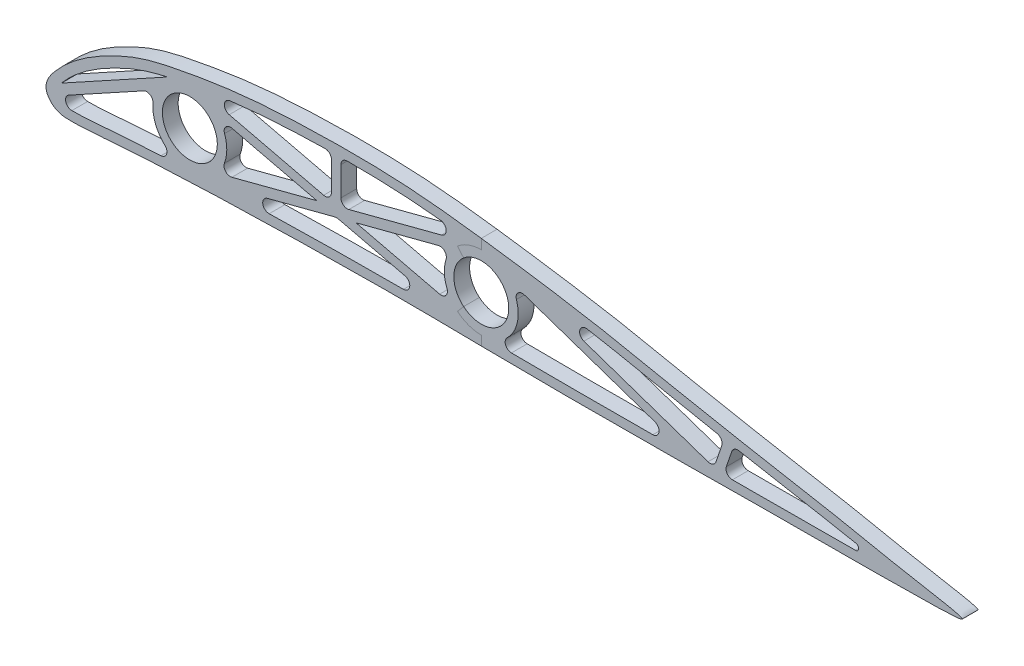
SolidWorks part; units mm, degrees
ref_plane "Front Plane" through (0, 0, 0) normal (0, 0, 1) x (1, 0, 0)
ref_plane "Top Plane" through (0, 0, 0) normal (0, 1, 0) x (1, 0, 0)
ref_plane "Right Plane" through (0, 0, 0) normal (1, 0, 0) x (0, 0, -1)
curve "Curve2"
  spline degree 3 poles (347.2078, -1.0359, 0) (378.9056, -0.7849, 0) (347.0347, 4.3271, 0) (326.8672, 8.8163, 0) (293.8899, 14.7227, 0) (257.5945, 21.3594, 0) (220.71, 29.3067, 0) (183.776, 34.7309, 0) (146.9268, 39.6342, 0) (109.9286, 39.8555, 0) (79.1221, 38.2217, 0) (54.6682, 34.1652, 0) (39.0987, 30.9157, 0) (27.0567, 25.6555, 0) (17.7869, 20.6913, 0) (10.0203, 15.09, 0) (3.6231, 8.8035, 0) (-2.539, 0.9573, 0) (3.8446, -5.5387, 0) (10.8213, -5.8955, 0) (18.4974, -5.5047, 0) (27.6862, -4.7118, 0) (39.9451, -3.8521, 0) (55.2855, -3.1527, 0) (79.8248, -2.2114, 0) (110.5105, -1.5148, 0) (147.3408, -1.1807, 0) (184.1821, -1.8502, 0) (220.968, -1.9589, 0) (257.9758, -1.783, 0) (294.1308, -1.2951, 0) (326.9075, -1.4474, 0) (347.2078, -1.0359, 0) (378.9056, -0.7849, 0) (347.0347, 4.3271, 0) knots -0.097522 -0.048769 -0.024396 0 0.025026 0.049952 0.099684 0.149416 0.199259 0.248703 0.297849 0.346623 0.395439 0.420071 0.445104 0.458263 0.47205 0.487006 0.495455 0.509299 0.518413 0.524589 0.536779 0.54899 0.561193 0.585585 0.609963 0.658715 0.707463 0.756228 0.804981 0.853734 0.902478 0.951231 0.975604 1 1.025026 1.049952 1.099684 periodic
sketch "Sketch2" plane through (0, 0, 0) normal (0, 0, 1) x (1, 0, 0)
  line L0 (336.0335, 6.748) -> (336.0335, 2.8594)
  line L2 (332.2235, 3.6512) -> (332.2235, 2.5181) construction
  line L3 (332.2235, 2.5181) -> (336.0335, 2.5612)
  line L4 (332.2235, 3.6512) -> (336.0335, 2.8594)
  line L5 (336.0335, 2.5612) -> (336.0335, -1.243)
  line L6 (336.0335, 6.748) -> (336.0335, -1.243) construction
  spline S0 degree 3 poles (347.2078, -1.0359) (378.9056, -0.7849) (347.0347, 4.3271) (326.8672, 8.8163) (293.8899, 14.7227) (257.5945, 21.3594) (220.71, 29.3067) (183.776, 34.7309) (146.9268, 39.6342) (109.9286, 39.8555) (79.1221, 38.2217) (54.6682, 34.1652) (39.0987, 30.9157) (27.0567, 25.6555) (17.7869, 20.6913) (10.0203, 15.09) (3.6231, 8.8035) (-2.539, 0.9573) (3.8446, -5.5387) (10.8213, -5.8955) (18.4974, -5.5047) (27.6862, -4.7118) (39.9451, -3.8521) (55.2855, -3.1527) (79.8248, -2.2114) (110.5105, -1.5148) (147.3408, -1.1807) (184.1821, -1.8502) (220.968, -1.9589) (257.9758, -1.783) (294.1308, -1.2951) (326.9075, -1.4474) (347.2078, -1.0359) (378.9056, -0.7849) (347.0347, 4.3271) knots -0.097522 -0.048769 -0.024396 0 0.025026 0.049952 0.099684 0.149416 0.199259 0.248703 0.297849 0.346623 0.395439 0.420071 0.445104 0.458263 0.47205 0.487006 0.495455 0.509299 0.518413 0.524589 0.536779 0.54899 0.561193 0.585585 0.609963 0.658715 0.707463 0.756228 0.804981 0.853734 0.902478 0.951231 0.975604 1 1.025026 1.049952 1.099684 only from (368.3, 0) to (368.3, 0) construction
  spline S1 degree 3 poles (336.0335, 6.748) (334.4682, 7.075) (322.1272, 9.6653) (293.8899, 14.7227) (257.5945, 21.3594) (220.71, 29.3067) (183.776, 34.7309) (146.9268, 39.6342) (109.9286, 39.8555) (79.1221, 38.2217) (54.6682, 34.1652) (39.0987, 30.9157) (27.0567, 25.6555) (17.7869, 20.6913) (10.0203, 15.09) (3.6231, 8.8035) (-2.539, 0.9573) (3.8446, -5.5387) (10.8213, -5.8955) (18.4974, -5.5047) (27.6862, -4.7118) (39.9451, -3.8521) (55.2855, -3.1527) (79.8248, -2.2114) (110.5105, -1.5148) (147.3408, -1.1807) (184.1821, -1.8502) (220.968, -1.9589) (257.9758, -1.783) (294.1308, -1.2951) (322.154, -1.4253) (334.5116, -1.2646) (336.0335, -1.243) knots 0.042905 0.042905 0.042905 0.042905 0.049952 0.099684 0.149416 0.199259 0.248703 0.297849 0.346623 0.395439 0.420071 0.445104 0.458263 0.47205 0.487006 0.495455 0.509299 0.518413 0.524589 0.536779 0.54899 0.561193 0.585585 0.609963 0.658715 0.707463 0.756228 0.804981 0.853734 0.902478 0.951231 0.95793 0.95793 0.95793 0.95793
  spline S2 degree 1 poles (332.2235, 3.6512) (332.2235, 2.5181) knots 0 0 1 1 construction
  spline S3 degree 3 poles (332.2235, 3.6512) (331.4422, 3.8136) (329.8922, 4.1334) (326.6834, 4.7813) (322.5372, 5.5957) (317.3751, 6.5801) (310.3118, 7.8973) (301.2497, 9.5464) (290.3993, 11.5032) (279.8146, 13.4324) (269.3583, 15.3818) (258.9524, 17.3888) (245.0217, 20.2063) (227.5735, 23.8306) (206.6663, 27.516) (185.5957, 30.5651) (164.4612, 33.491) (143.4609, 35.515) (125.8553, 35.9183) (111.6987, 35.7516) (97.5326, 35.338) (83.4604, 34.4409) (69.558, 32.7373) (59.1489, 31.0158) (48.6966, 29.0654) (40.4092, 26.9524) (34.112, 24.5762) (29.4067, 22.4489) (24.7943, 20.1232) (20.3602, 17.5841) (16.7827, 15.2133) (14.0746, 13.1936) (12.14, 11.6239) (10.3374, 10.022) (8.8926, 8.6048) (7.7177, 7.3643) (6.5041, 6.0281) (5.094, 4.3284) (4.135, 2.7508) (3.7669, 1.7737) (3.6718, 1.2421) (3.687, 0.9354) (3.7569, 0.6641) (4.0378, 0.131) (4.6772, -0.6496) (5.6338, -1.3432) (6.4413, -1.6604) (7.2188, -1.8332) (8.1959, -1.9275) (9.4011, -1.9594) (10.6859, -1.9678) (12.3801, -1.9489) (14.5213, -1.8763) (17.9805, -1.6803) (22.3734, -1.3453) (27.7107, -0.9045) (34.8675, -0.3821) (43.8089, 0.1382) (54.5116, 0.6135) (65.1973, 1.0423) (75.8958, 1.4157) (86.5937, 1.7244) (100.8575, 2.0599) (118.6805, 2.3593) (140.0876, 2.5332) (161.5153, 2.3652) (182.8671, 2.0367) (204.1695, 1.8943) (225.5342, 1.8895) (243.3798, 1.9622) (257.562, 2.0721) (268.1295, 2.1811) (278.734, 2.2927) (289.4592, 2.3847) (300.4526, 2.4262) (309.6907, 2.428) (316.9209, 2.4346) (322.2225, 2.4467) (326.4945, 2.4674) (329.8143, 2.493) (331.4156, 2.509) (332.2235, 2.5181) knots 0.047492 0.047492 0.047492 0.047492 0.051027 0.054562 0.061631 0.0687 0.07577 0.089908 0.104047 0.118186 0.132325 0.146463 0.160602 0.18888 0.217157 0.245434 0.273712 0.301989 0.330267 0.344405 0.358544 0.386822 0.40096 0.415099 0.429238 0.443376 0.450446 0.457515 0.464585 0.471654 0.478723 0.482258 0.485793 0.489327 0.492862 0.494629 0.496397 0.499931 0.503466 0.505233 0.507001 0.508768 0.510535 0.512303 0.51407 0.517605 0.519372 0.521139 0.522907 0.524674 0.526441 0.528209 0.531743 0.535278 0.542347 0.549417 0.556486 0.570625 0.584764 0.598902 0.613041 0.62718 0.641319 0.669596 0.697873 0.726151 0.754428 0.782706 0.810983 0.839261 0.853399 0.867538 0.881677 0.895815 0.909954 0.924093 0.931162 0.938232 0.945301 0.948836 0.95237 0.95237 0.95237 0.95237
  dimension "D2" = 3.81
extrude "MainRibEdge" add sketch "Sketch2" along normal blind 6.35
sketch "Sketch3" plane through (0, 0, 6.35) normal (0, 0, 1) x (1, 0, 0)
  line L0 (336.0335, 6.748) -> (336.0335, -1.243)
  spline S0 degree 3 poles (347.2078, -1.0359) (378.9056, -0.7849) (347.0347, 4.3271) (326.8672, 8.8163) (293.8899, 14.7227) (257.5945, 21.3594) (220.71, 29.3067) (183.776, 34.7309) (146.9268, 39.6342) (109.9286, 39.8555) (79.1221, 38.2217) (54.6682, 34.1652) (39.0987, 30.9157) (27.0567, 25.6555) (17.7869, 20.6913) (10.0203, 15.09) (3.6231, 8.8035) (-2.539, 0.9573) (3.8446, -5.5387) (10.8213, -5.8955) (18.4974, -5.5047) (27.6862, -4.7118) (39.9451, -3.8521) (55.2855, -3.1527) (79.8248, -2.2114) (110.5105, -1.5148) (147.3408, -1.1807) (184.1821, -1.8502) (220.968, -1.9589) (257.9758, -1.783) (294.1308, -1.2951) (326.9075, -1.4474) (347.2078, -1.0359) (378.9056, -0.7849) (347.0347, 4.3271) knots -0.097522 -0.048769 -0.024396 0 0.025026 0.049952 0.099684 0.149416 0.199259 0.248703 0.297849 0.346623 0.395439 0.420071 0.445104 0.458263 0.47205 0.487006 0.495455 0.509299 0.518413 0.524589 0.536779 0.54899 0.561193 0.585585 0.609963 0.658715 0.707463 0.756228 0.804981 0.853734 0.902478 0.951231 0.975604 1 1.025026 1.049952 1.099684 only from (368.3, 0) to (368.3, 0) construction
  spline S1 degree 3 poles (336.0335, -1.243) (340.0487, -1.1859) (350.0854, -1.0131) (378.9056, -0.7849) (350.0555, 3.8426) (340.005, 5.9184) (336.0335, 6.748) knots 0.95793 0.95793 0.95793 0.95793 0.975604 1 1.025026 1.042905 1.042905 1.042905 1.042905
extrude "TrailingEdge" add sketch "Sketch3" against normal blind 6.35
curve "Curve3"
  spline degree 3 poles (368.3, 0, 0) (362.1489, 1.3722, 0) (349.8713, 4.1111, 0) (325.2364, 8.9405, 0) (294.4435, 14.6806, 0) (257.4457, 21.3707, 0) (220.7495, 29.3036, 0) (183.7655, 34.7317, 0) (146.9295, 39.6339, 0) (109.9284, 39.8556, 0) (79.1207, 38.2216, 0) (54.6708, 34.1654, 0) (39.0905, 30.9151, 0) (27.0719, 25.6565, 0) (17.7236, 20.6872, 0) (10.231, 15.1036, 0) (3.1002, 8.7697, 0) (1.1877, 3.3596, 0) (0, 0, 0) knots 0 0 0 0 0.049139 0.09808 0.195728 0.293375 0.391241 0.488324 0.584822 0.680589 0.776437 0.824803 0.873954 0.899793 0.926862 0.956228 0.972818 1 1 1 1
curve "Curve4"
  spline degree 3 poles (0, 0, 0) (1.3411, -2.0747, 0) (3.5909, -5.5551, 0) (10.9428, -5.8876, 0) (18.4563, -5.5073, 0) (27.697, -4.7111, 0) (39.9389, -3.8525, 0) (55.2876, -3.1526, 0) (79.8237, -2.2115, 0) (110.5102, -1.5147, 0) (147.3434, -1.1809, 0) (184.1719, -1.8495, 0) (221.006, -1.9618, 0) (257.8337, -1.7722, 0) (294.6611, -1.3355, 0) (325.3463, -1.3285, 0) (349.9126, -1.2419, 0) (362.169, -0.4141, 0) (368.3, 0, 0) knots 0 0 0 0 0.018575 0.03116 0.056003 0.080886 0.105755 0.155463 0.205144 0.304495 0.40384 0.503218 0.602571 0.701924 0.80126 0.900613 0.950284 1 1 1 1
sketch "Sketch4" plane through (0, 0, 6.35) normal (0, 0, 1) x (1, 0, 0)
  circle A0 centre (57.717, 15.6105) radius 11.049
  circle A1 centre (57.717, 15.6105) radius 14.859
  circle A2 centre (174.9061, 17.0255) radius 11.049
  circle A4 centre (174.9061, 17.0255) radius 14.859
  spline S2 degree 3 poles (-1571.0958, -3668.5405) (-88.2173, 232.2354) (-14.5428, 28.2276) (4.264, 0.4587) (4.5107, 0.113) (4.9792, -0.4876) (5.2009, -0.742) (5.6043, -1.1472) (5.7849, -1.2973) (6.0163, -1.4571) (6.0869, -1.4998) (6.218, -1.5696) (6.2738, -1.5952) (6.5055, -1.6837) (6.7297, -1.7469) (7.3085, -1.8487) (7.6611, -1.8872) (8.4582, -1.9367) (8.9036, -1.948) (11.2732, -1.982) (13.1149, -1.9349) (15.8918, -1.8) (16.8198, -1.7443) (18.6946, -1.6194) (19.6412, -1.5506) (22.497, -1.3333) (24.4247, -1.1735) (27.3326, -0.9419) (28.3045, -0.8665) (30.2445, -0.7212) (31.2138, -0.651) (36.0591, -0.3127) (39.9362, -0.0847) (47.6854, 0.3119) (51.5566, 0.4823) (59.2863, 0.8059) (63.1514, 0.9589) (74.7494, 1.3838) (82.4858, 1.6176) (97.9554, 1.9959) (105.6888, 2.1426) (121.1575, 2.3706) (128.8957, 2.4488) (140.5079, 2.4812) (144.3799, 2.4777) (152.1235, 2.4375) (155.9925, 2.4015) (167.5916, 2.27) (175.3135, 2.1512) (190.7368, 1.9806) (198.448, 1.932) (213.8764, 1.8885) (221.5928, 1.8927) (237.026, 1.9369) (244.743, 1.9781) (260.1775, 2.094) (267.8962, 2.1724) (283.345, 2.3207) (291.0761, 2.3883) (306.5365, 2.463) (316.1941, 2.4798) (325.8471, 2.4976) (329.7079, 2.5056) (331.6394, 2.5096) (337.4218, 2.5273) (341.2613, 2.5504) (346.9942, 2.6712) (348.8987, 2.726) (352.7083, 2.8747) (354.6165, 2.9673) (526.3996, 12.3921) (724.4042, 119.0773) (1102.622, -3899.0392) knots -0.277791 -0.277791 -0.277791 -0.277791 0.003906 0.003906 0.007813 0.007813 0.011719 0.011719 0.015625 0.015625 0.017578 0.017578 0.019531 0.019531 0.023438 0.023438 0.027344 0.027344 0.03125 0.03125 0.046875 0.046875 0.054688 0.054688 0.0625 0.0625 0.078125 0.078125 0.085938 0.085938 0.09375 0.09375 0.125 0.125 0.15625 0.15625 0.1875 0.1875 0.25 0.25 0.3125 0.3125 0.375 0.375 0.40625 0.40625 0.4375 0.4375 0.5 0.5 0.5625 0.5625 0.625 0.625 0.6875 0.6875 0.75 0.75 0.8125 0.8125 0.875 0.890625 0.890625 0.90625 0.90625 0.9375 0.9375 0.953125 0.953125 0.96875 0.96875 2.357133 2.357133 2.357133 2.357133 only from (3.1997, 2.0683) to (368.0433, 3.8013)
  spline S3 degree 3 poles (3.1997, 2.0683) (3.4817, 1.632) (3.7496, 1.2183) (4.264, 0.4587) (4.5107, 0.113) (4.9792, -0.4876) (5.2009, -0.742) (5.6043, -1.1472) (5.7849, -1.2973) (6.0163, -1.4571) (6.0869, -1.4998) (6.218, -1.5696) (6.2738, -1.5952) (6.5055, -1.6837) (6.7297, -1.7469) (7.3085, -1.8487) (7.6611, -1.8872) (8.4582, -1.9367) (8.9036, -1.948) (11.2732, -1.982) (13.1149, -1.9349) (15.8918, -1.8) (16.8198, -1.7443) (18.6946, -1.6194) (19.6412, -1.5506) (22.497, -1.3333) (24.4247, -1.1735) (27.3326, -0.9419) (28.3045, -0.8665) (30.2445, -0.7212) (31.2138, -0.651) (36.0591, -0.3127) (39.9362, -0.0847) (47.6854, 0.3119) (51.5566, 0.4823) (59.2863, 0.8059) (63.1514, 0.9589) (74.7494, 1.3838) (82.4858, 1.6176) (97.9554, 1.9959) (105.6888, 2.1426) (121.1575, 2.3706) (128.8957, 2.4488) (140.5079, 2.4812) (144.3799, 2.4777) (152.1235, 2.4375) (155.9925, 2.4015) (167.5916, 2.27) (175.3135, 2.1512) (190.7368, 1.9806) (198.448, 1.932) (213.8764, 1.8885) (221.5928, 1.8927) (237.026, 1.9369) (244.743, 1.9781) (260.1775, 2.094) (267.8962, 2.1724) (283.345, 2.3207) (291.0761, 2.3883) (306.5365, 2.463) (316.1941, 2.4798) (325.8471, 2.4976) (329.7079, 2.5056) (331.6394, 2.5096) (337.4218, 2.5273) (341.2613, 2.5504) (346.9942, 2.6712) (348.8987, 2.726) (352.7083, 2.8747) (354.6165, 2.9673) (360.3518, 3.282) (364.1895, 3.5411) (368.0433, 3.8013) knots 0 0 0 0 0.003906 0.003906 0.007813 0.007813 0.011719 0.011719 0.015625 0.015625 0.017578 0.017578 0.019531 0.019531 0.023438 0.023438 0.027344 0.027344 0.03125 0.03125 0.046875 0.046875 0.054688 0.054688 0.0625 0.0625 0.078125 0.078125 0.085938 0.085938 0.09375 0.09375 0.125 0.125 0.15625 0.15625 0.1875 0.1875 0.25 0.25 0.3125 0.3125 0.375 0.375 0.40625 0.40625 0.4375 0.4375 0.5 0.5 0.5625 0.5625 0.625 0.625 0.6875 0.6875 0.75 0.75 0.8125 0.8125 0.875 0.890625 0.890625 0.90625 0.90625 0.9375 0.9375 0.953125 0.953125 0.96875 0.96875 1 1 1 1 construction
  spline S4 degree 3 poles (1901.0031, 3637.0886) (816.3443, -173.7195) (582.3534, -50.4293) (353.7985, -0.7009) (351.8475, -0.2818) (347.9455, 0.5405) (345.993, 0.9434) (340.1258, 2.1338) (336.204, 2.9029) (328.3466, 4.4231) (324.4137, 5.1752) (312.613, 7.4121) (304.7392, 8.8774) (288.9826, 11.7783) (281.0944, 13.2096) (269.2557, 15.4211) (265.3088, 16.1692) (257.4168, 17.7031) (253.4715, 18.4933) (241.6703, 20.8929) (233.8353, 22.5229) (222.0886, 24.7697) (218.1759, 25.4814) (210.3248, 26.8249) (202.4536, 28.0955) (192.5729, 29.5555) (186.6295, 30.3981) (182.6644, 30.9552) (180.681, 31.2319) (170.7744, 32.5931) (162.8689, 33.6082) (153.0009, 34.5508) (151.028, 34.723) (147.0834, 35.0291) (145.112, 35.1623) (139.1878, 35.503) (131.2697, 35.8036) (121.3334, 35.8636) (115.3586, 35.7886) (111.3731, 35.7174) (109.3783, 35.6716) (99.4154, 35.3927) (91.4736, 35.0002) (81.624, 34.1164) (79.658, 33.92) (75.7347, 33.4834) (73.7788, 33.2431) (67.9144, 32.4509) (63.031, 31.6763) (58.1403, 30.7993) (56.1832, 30.4412) (55.2029, 30.2586) (52.2756, 29.7009) (50.3406, 29.3138) (46.5207, 28.4683) (44.636, 28.0099) (41.859, 27.2394) (40.9417, 26.9688) (39.1257, 26.3954) (38.2286, 26.0931) (35.557, 25.1274) (33.7867, 24.402) (31.1413, 23.2238) (30.2612, 22.8161) (28.5034, 21.9764) (27.628, 21.5462) (25.0351, 20.2287) (23.3443, 19.3106) (20.8878, 17.8531) (20.0841, 17.3547) (18.4955, 16.3224) (17.7104, 15.7891) (15.3782, 14.1396) (13.6639, 12.8283) (11.9755, 11.4415) (11.6009, 11.1315) (11.4132, 10.975) (10.8587, 10.5089) (10.4997, 10.2013) (9.4655, 9.2841) (8.834, 8.6794) (8.0104, 7.7755) (7.7562, 7.4748) (7.2921, 6.8738) (7.0717, 6.5599) (6.432, 5.5658) (6.0381, 4.8371) (5.2946, 3.2613) (4.9454, 2.4147) (-14.5896, -48.7628) (-5.3634, -241.0265) (-3366.7369, 2137.3538) knots -1.783016 -1.783016 -1.783016 -1.783016 0.03125 0.03125 0.046875 0.046875 0.0625 0.0625 0.09375 0.09375 0.125 0.125 0.1875 0.1875 0.25 0.25 0.28125 0.28125 0.3125 0.3125 0.375 0.375 0.40625 0.40625 0.4375 0.46875 0.484375 0.484375 0.5 0.5 0.5625 0.5625 0.578125 0.578125 0.59375 0.59375 0.625 0.65625 0.671875 0.671875 0.6875 0.6875 0.75 0.75 0.765625 0.765625 0.78125 0.78125 0.8125 0.820313 0.820313 0.828125 0.828125 0.84375 0.84375 0.859375 0.859375 0.867188 0.867188 0.875 0.875 0.890625 0.890625 0.898438 0.898438 0.90625 0.90625 0.921875 0.921875 0.929688 0.929688 0.9375 0.9375 0.953125 0.955078 0.955078 0.957031 0.957031 0.960938 0.960938 0.96875 0.96875 0.972656 0.972656 0.976562 0.976562 0.984375 0.984375 0.992188 0.992188 1.432876 1.432876 1.432876 1.432876 only from (367.4705, -3.7186) to (3.5921, -1.2699)
  spline S5 degree 3 poles (367.4705, -3.7186) (363.5586, -2.8459) (357.7006, -1.5392) (351.8475, -0.2818) (347.9455, 0.5405) (345.993, 0.9434) (340.1258, 2.1338) (336.204, 2.9029) (328.3466, 4.4231) (324.4137, 5.1752) (312.613, 7.4121) (304.7392, 8.8774) (288.9826, 11.7783) (281.0944, 13.2096) (269.2557, 15.4211) (265.3088, 16.1692) (257.4168, 17.7031) (253.4715, 18.4933) (241.6703, 20.8929) (233.8353, 22.5229) (222.0886, 24.7697) (218.1759, 25.4814) (210.3248, 26.8249) (202.4536, 28.0955) (192.5729, 29.5555) (186.6295, 30.3981) (182.6644, 30.9552) (180.681, 31.2319) (170.7744, 32.5931) (162.8689, 33.6082) (153.0009, 34.5508) (151.028, 34.723) (147.0834, 35.0291) (145.112, 35.1623) (139.1878, 35.503) (131.2697, 35.8036) (121.3334, 35.8636) (115.3586, 35.7886) (111.3731, 35.7174) (109.3783, 35.6716) (99.4154, 35.3927) (91.4736, 35.0002) (81.624, 34.1164) (79.658, 33.92) (75.7347, 33.4834) (73.7788, 33.2431) (67.9144, 32.4509) (63.031, 31.6763) (58.1403, 30.7993) (56.1832, 30.4412) (55.2029, 30.2586) (52.2756, 29.7009) (50.3406, 29.3138) (46.5207, 28.4683) (44.636, 28.0099) (41.859, 27.2394) (40.9417, 26.9688) (39.1257, 26.3954) (38.2286, 26.0931) (35.557, 25.1274) (33.7867, 24.402) (31.1413, 23.2238) (30.2612, 22.8161) (28.5034, 21.9764) (27.628, 21.5462) (25.0351, 20.2287) (23.3443, 19.3106) (20.8878, 17.8531) (20.0841, 17.3547) (18.4955, 16.3224) (17.7104, 15.7891) (15.3782, 14.1396) (13.6639, 12.8283) (11.9755, 11.4415) (11.6009, 11.1315) (11.4132, 10.975) (10.8587, 10.5089) (10.4997, 10.2013) (9.4655, 9.2841) (8.834, 8.6794) (8.0104, 7.7755) (7.7562, 7.4748) (7.2921, 6.8738) (7.0717, 6.5599) (6.432, 5.5658) (6.0381, 4.8371) (5.2946, 3.2613) (4.9454, 2.4147) (4.2648, 0.6318) (3.9335, -0.3043) (3.5921, -1.2699) knots 0 0 0 0 0.03125 0.046875 0.046875 0.0625 0.0625 0.09375 0.09375 0.125 0.125 0.1875 0.1875 0.25 0.25 0.28125 0.28125 0.3125 0.3125 0.375 0.375 0.40625 0.40625 0.4375 0.46875 0.484375 0.484375 0.5 0.5 0.5625 0.5625 0.578125 0.578125 0.59375 0.59375 0.625 0.65625 0.671875 0.671875 0.6875 0.6875 0.75 0.75 0.765625 0.765625 0.78125 0.78125 0.8125 0.820313 0.820313 0.828125 0.828125 0.84375 0.84375 0.859375 0.859375 0.867188 0.867188 0.875 0.875 0.890625 0.890625 0.898438 0.898438 0.90625 0.90625 0.921875 0.921875 0.929688 0.929688 0.9375 0.9375 0.953125 0.955078 0.955078 0.957031 0.957031 0.960938 0.960938 0.96875 0.96875 0.972656 0.972656 0.976562 0.976562 0.984375 0.984375 0.992188 0.992188 1 1 1 1 construction
  point P12 (58.3209, 0.7638)
  point P14 (54.9652, 30.2125)
  point P15 (174.7116, 2.1678)
  point P16 (176.9071, 31.7492)
  dimension "D3" = 22.098
  dimension "D5" = 22.098
  dimension "D1" = 3.81
  dimension "D2" = 3.81
  dimension "D4" = 3.81
  dimension "D6" = 3.81
extrude "SparHoles" add sketch "Sketch4" against normal blind 6.35
sketch "Sketch5" plane through (0, 0, 6.35) normal (0, 0, 1) x (1, 0, 0)
  line L0 (56.7665, 32.2492) -> (114.6518, 18.447)
  line L2 (175.1534, 4.0209) -> (174.2697, 0.3148)
  line L3 (55.8829, 28.5431) -> (108.806, 15.924)
  line L4 (56.7665, 32.2492) -> (174.2697, 0.3148) construction
  line L5 (175.1534, 4.0209) -> (55.8829, 28.5431) construction
  line L6 (57.8394, 2.6069) -> (108.806, 15.924)
  line L7 (57.8394, 2.6069) -> (58.8025, -1.0793)
  line L8 (176.4256, 33.5923) -> (177.3887, 29.9061) construction
  line L9 (58.8025, -1.0793) -> (116.6861, 14.0451)
  line L10 (57.8394, 2.6069) -> (177.3887, 29.9061) construction
  line L11 (176.4256, 33.5923) -> (58.8025, -1.0793) construction
  line L12 (116.6861, 14.0451) -> (174.2697, 0.3148)
  line L13 (124.5239, 16.093) -> (177.3887, 29.9061)
  line L14 (124.5239, 16.093) -> (175.1534, 4.0209)
  line L15 (118.4618, 18.447) -> (176.4256, 33.5923)
  line L16 (54.0476, 31.8819) -> (1.3083, 2.8929)
  line L17 (54.0476, 31.8819) -> (55.8829, 28.5431) construction
  line L18 (1.3083, 2.8929) -> (3.1435, -0.4459)
  line L19 (55.8829, 28.5431) -> (3.1435, -0.4459)
  line L20 (54.0476, 31.8819) -> (3.1435, -0.4459) construction
  line L21 (1.3083, 2.8929) -> (55.8829, 28.5431) construction
  line L22 (0, 0) -> (54.9652, 30.2125) construction
  line L23 (54.0476, 31.8819) -> (56.7665, 32.2492)
  line L24 (114.6518, 18.447) -> (114.6518, 35.7739)
  line L25 (176.9071, 31.7492) -> (263.6116, 2.1312) construction
  line L26 (177.3887, 29.9061) -> (258.8242, 2.088)
  line L27 (188.5246, 30.1282) -> (270.2971, 2.195)
  line L28 (176.4256, 33.5923) -> (188.5246, 30.1282)
  line L29 (258.8242, 2.088) -> (258.8242, -0.452)
  line L30 (258.8242, -0.452) -> (270.2971, -0.345)
  line L31 (270.2971, -0.345) -> (270.2971, 2.195)
  line L32 (118.4618, 18.447) -> (118.4618, 35.8192)
  line L34 (114.6518, 35.7739) -> (114.6518, 37.0439)
  line L35 (114.6518, 37.0439) -> (118.4618, 37.0439)
  line L36 (118.4618, 37.0439) -> (118.4618, 35.8192)
  spline S0 degree 3 poles (58.2648, 0.7616) (57.013, 0.7107) (52.1973, 0.5107) (43.8089, 0.1382) (34.8675, -0.3821) (27.7107, -0.9045) (22.3734, -1.3453) (17.9805, -1.6803) (14.5213, -1.8763) (12.3801, -1.9489) (10.6859, -1.9678) (9.4011, -1.9594) (8.1959, -1.9275) (7.2188, -1.8332) (6.4413, -1.6604) (5.6338, -1.3432) (4.6772, -0.6496) (4.0378, 0.131) (3.7569, 0.6641) (3.687, 0.9354) (3.6718, 1.2421) (3.7669, 1.7737) (4.135, 2.7508) (5.094, 4.3284) (6.5041, 6.0281) (7.7177, 7.3643) (8.8926, 8.6048) (10.3374, 10.022) (12.14, 11.6239) (14.0746, 13.1936) (16.7827, 15.2133) (20.3602, 17.5841) (24.7943, 20.1232) (29.4067, 22.4489) (34.112, 24.5762) (40.4092, 26.9524) (48.6966, 29.0654) (59.1489, 31.0158) (69.558, 32.7373) (83.4604, 34.4409) (97.5326, 35.338) (111.6987, 35.7516) (125.8553, 35.9183) (143.4609, 35.515) (164.4612, 33.491) (185.5957, 30.5651) (206.6663, 27.516) (227.5735, 23.8306) (245.0217, 20.2063) (258.9524, 17.3888) (269.3583, 15.3818) (279.8146, 13.4324) (290.3993, 11.5032) (301.2497, 9.5464) (310.3118, 7.8973) (317.3751, 6.5801) (322.5372, 5.5957) (326.6834, 4.7813) (329.8922, 4.1334) (331.4422, 3.8136) (332.2235, 3.6512) knots 0.410132 0.410132 0.410132 0.410132 0.415099 0.429238 0.443376 0.450446 0.457515 0.464585 0.468119 0.471654 0.473421 0.475189 0.476956 0.478723 0.480491 0.482258 0.485793 0.48756 0.489327 0.491095 0.492862 0.494629 0.496397 0.499931 0.503466 0.505233 0.507001 0.510535 0.51407 0.517605 0.521139 0.528209 0.535278 0.542347 0.549417 0.556486 0.570625 0.584764 0.598902 0.613041 0.641319 0.655457 0.669596 0.697873 0.726151 0.754428 0.782706 0.810983 0.839261 0.853399 0.867538 0.881677 0.895815 0.909954 0.924093 0.931162 0.938232 0.945301 0.948836 0.95237 0.95237 0.95237 0.95237 construction
  spline S3 degree 3 poles (3.1997, 2.0683) (3.4817, 1.632) (3.7496, 1.2183) (4.264, 0.4587) (4.5107, 0.113) (4.9792, -0.4876) (5.2009, -0.742) (5.6043, -1.1472) (5.7849, -1.2973) (6.0163, -1.4571) (6.0869, -1.4998) (6.218, -1.5696) (6.2738, -1.5952) (6.5055, -1.6837) (6.7297, -1.7469) (7.3085, -1.8487) (7.6611, -1.8872) (8.4582, -1.9367) (8.9036, -1.948) (11.2732, -1.982) (13.1149, -1.9349) (15.8918, -1.8) (16.8198, -1.7443) (18.6946, -1.6194) (19.6412, -1.5506) (22.497, -1.3333) (24.4247, -1.1735) (27.3326, -0.9419) (28.3045, -0.8665) (30.2445, -0.7212) (31.2138, -0.651) (36.0591, -0.3127) (39.9362, -0.0847) (47.6854, 0.3119) (51.5566, 0.4823) (59.2863, 0.8059) (63.1514, 0.9589) (74.7494, 1.3838) (82.4858, 1.6176) (97.9554, 1.9959) (105.6888, 2.1426) (121.1575, 2.3706) (128.8957, 2.4488) (140.5079, 2.4812) (144.3799, 2.4777) (152.1235, 2.4375) (155.9925, 2.4015) (167.5916, 2.27) (175.3135, 2.1512) (190.7368, 1.9806) (198.448, 1.932) (213.8764, 1.8885) (221.5928, 1.8927) (237.026, 1.9369) (244.743, 1.9781) (260.1775, 2.094) (267.8962, 2.1724) (283.345, 2.3207) (291.0761, 2.3883) (306.5365, 2.463) (316.1941, 2.4798) (325.8471, 2.4976) (329.7079, 2.5056) (331.6394, 2.5096) (337.4218, 2.5273) (341.2613, 2.5504) (346.9942, 2.6712) (348.8987, 2.726) (352.7083, 2.8747) (354.6165, 2.9673) (360.3518, 3.282) (364.1895, 3.5411) (368.0433, 3.8013) knots 0 0 0 0 0.003906 0.003906 0.007813 0.007813 0.011719 0.011719 0.015625 0.015625 0.017578 0.017578 0.019531 0.019531 0.023438 0.023438 0.027344 0.027344 0.03125 0.03125 0.046875 0.046875 0.054688 0.054688 0.0625 0.0625 0.078125 0.078125 0.085938 0.085938 0.09375 0.09375 0.125 0.125 0.15625 0.15625 0.1875 0.1875 0.25 0.25 0.3125 0.3125 0.375 0.375 0.40625 0.40625 0.4375 0.4375 0.5 0.5 0.5625 0.5625 0.625 0.625 0.6875 0.6875 0.75 0.75 0.8125 0.8125 0.875 0.890625 0.890625 0.90625 0.90625 0.9375 0.9375 0.953125 0.953125 0.96875 0.96875 1 1 1 1 construction
  spline S4 degree 3 poles (367.4705, -3.7186) (363.5586, -2.8459) (357.7006, -1.5392) (351.8475, -0.2818) (347.9455, 0.5405) (345.993, 0.9434) (340.1258, 2.1338) (336.204, 2.9029) (328.3466, 4.4231) (324.4137, 5.1752) (312.613, 7.4121) (304.7392, 8.8774) (288.9826, 11.7783) (281.0944, 13.2096) (269.2557, 15.4211) (265.3088, 16.1692) (257.4168, 17.7031) (253.4715, 18.4933) (241.6703, 20.8929) (233.8353, 22.5229) (222.0886, 24.7697) (218.1759, 25.4814) (210.3248, 26.8249) (202.4536, 28.0955) (192.5729, 29.5555) (186.6295, 30.3981) (182.6644, 30.9552) (180.681, 31.2319) (170.7744, 32.5931) (162.8689, 33.6082) (153.0009, 34.5508) (151.028, 34.723) (147.0834, 35.0291) (145.112, 35.1623) (139.1878, 35.503) (131.2697, 35.8036) (121.3334, 35.8636) (115.3586, 35.7886) (111.3731, 35.7174) (109.3783, 35.6716) (99.4154, 35.3927) (91.4736, 35.0002) (81.624, 34.1164) (79.658, 33.92) (75.7347, 33.4834) (73.7788, 33.2431) (67.9144, 32.4509) (63.031, 31.6763) (58.1403, 30.7993) (56.1832, 30.4412) (55.2029, 30.2586) (52.2756, 29.7009) (50.3406, 29.3138) (46.5207, 28.4683) (44.636, 28.0099) (41.859, 27.2394) (40.9417, 26.9688) (39.1257, 26.3954) (38.2286, 26.0931) (35.557, 25.1274) (33.7867, 24.402) (31.1413, 23.2238) (30.2612, 22.8161) (28.5034, 21.9764) (27.628, 21.5462) (25.0351, 20.2287) (23.3443, 19.3106) (20.8878, 17.8531) (20.0841, 17.3547) (18.4955, 16.3224) (17.7104, 15.7891) (15.3782, 14.1396) (13.6639, 12.8283) (11.9755, 11.4415) (11.6009, 11.1315) (11.4132, 10.975) (10.8587, 10.5089) (10.4997, 10.2013) (9.4655, 9.2841) (8.834, 8.6794) (8.0104, 7.7755) (7.7562, 7.4748) (7.2921, 6.8738) (7.0717, 6.5599) (6.432, 5.5658) (6.0381, 4.8371) (5.2946, 3.2613) (4.9454, 2.4147) (4.2648, 0.6318) (3.9335, -0.3043) (3.5921, -1.2699) knots 0 0 0 0 0.03125 0.046875 0.046875 0.0625 0.0625 0.09375 0.09375 0.125 0.125 0.1875 0.1875 0.25 0.25 0.28125 0.28125 0.3125 0.3125 0.375 0.375 0.40625 0.40625 0.4375 0.46875 0.484375 0.484375 0.5 0.5 0.5625 0.5625 0.578125 0.578125 0.59375 0.59375 0.625 0.65625 0.671875 0.671875 0.6875 0.6875 0.75 0.75 0.765625 0.765625 0.78125 0.78125 0.8125 0.820313 0.820313 0.828125 0.828125 0.84375 0.84375 0.859375 0.859375 0.867188 0.867188 0.875 0.875 0.890625 0.890625 0.898438 0.898438 0.90625 0.90625 0.921875 0.921875 0.929688 0.929688 0.9375 0.9375 0.953125 0.955078 0.955078 0.957031 0.957031 0.960938 0.960938 0.96875 0.96875 0.972656 0.972656 0.976562 0.976562 0.984375 0.984375 0.992188 0.992188 1 1 1 1 construction
  point P0 (174.7116, 2.1678)
  point P1 (115.5181, 16.282)
  point P3 (176.9071, 31.7492)
  point P10 (117.614, 16.2565)
  point P11 (58.3209, 0.7638)
  point P22 (54.9652, 30.2125)
  point P26 (28.5956, 15.718)
  point P34 (2.2259, 1.2235)
  dimension "D1" = 3.81
  dimension "D2" = 3.81
  dimension "D3" = 3.81
  dimension "D4" = 2.54
  dimension "D5" = 3.81
  dimension "D6" = 88.9
  dimension "D7" = 3.81
  dimension "D8" = 2.54
  dimension "D9" = 2.54
  dimension "D10" = 3.81
  dimension "D11" = 1.27
extrude "Reinforcements" add sketch "Sketch5" against normal blind 6.35
sketch "Sketch7" plane through (28.9161, 84.65, 0) normal (0.3233, 0.9463, 0) x (0.9463, -0.3233, 0)
  line L0 (255.0484, 0) -> (255.0484, -6.35) construction
  line L1 (256.9534, 0) -> (253.1434, 0)
  line L2 (256.9534, 0) -> (256.9534, -6.35)
  line L3 (256.9534, -6.35) -> (253.1434, -6.35)
  line L4 (253.1434, 0) -> (253.1434, -6.35)
  line L5 (256.9534, 0) -> (253.1434, -6.35) construction
  line L6 (256.9534, -6.35) -> (253.1434, 0) construction
  line L7 (255.0484, -6.35) -> (168.6709, -6.35) construction
  point P0 (255.0484, -3.175)
  dimension "D1" = 3.81
extrude "RearReinforcementAddition" add sketch "Sketch7" along normal up to next
sketch "Sketch9" plane through (0, 0, 6.35) normal (0, 0, 1) x (1, 0, 0)
  line L4 (276.3421, 14.0824) -> (272.2916, 2.2248)
  line L5 (336.0335, 2.8594) -> (332.2235, 3.6512)
  line L6 (336.0335, 2.5612) -> (336.0335, 2.8594)
  line L7 (332.2235, 2.5181) -> (336.0335, 2.5612)
  line L9 (336.0335, 2.8594) -> (332.2235, 3.6512)
  line L10 (336.0335, 2.5612) -> (336.0335, 2.8594)
  line L11 (332.2235, 2.5181) -> (336.0335, 2.5612)
  arc A0 (325.6677, 4.9791) -> (325.4285, 2.4631) centre (325.4217, 3.7331) cw
  spline S0 degree 3 poles (276.3421, 14.0824) (277.5047, 13.8663) (282.1689, 13.0033) (290.3993, 11.5032) (301.2497, 9.5464) (310.3118, 7.8973) (317.3751, 6.5801) (322.5372, 5.5957) (326.6834, 4.7813) (329.8922, 4.1334) (331.4422, 3.8136) (332.2235, 3.6512) knots 0.876972 0.876972 0.876972 0.876972 0.881677 0.895815 0.909954 0.924093 0.931162 0.938232 0.945301 0.948836 0.95237 0.95237 0.95237 0.95237 construction
  spline S1 degree 3 poles (332.2235, 2.5181) (331.4156, 2.509) (329.8143, 2.493) (326.4945, 2.4674) (322.2225, 2.4467) (316.9209, 2.4346) (309.6907, 2.428) (300.4526, 2.4262) (289.4592, 2.3847) (280.1363, 2.3048) (274.4404, 2.247) (272.2916, 2.2248) knots 0.047492 0.047492 0.047492 0.047492 0.051027 0.054562 0.061631 0.0687 0.07577 0.089908 0.104047 0.118186 0.126779 0.126779 0.126779 0.126779 construction
  spline S4 degree 3 poles (3284.4349, -527.7093) (375.1974, -9.9931) (371.4332, -4.2539) (326.6834, 4.7813) (322.5372, 5.5957) (317.3751, 6.5801) (310.3118, 7.8973) (301.2497, 9.5464) (290.3993, 11.5032) (84.2174, 49.0824) (-47.842, 97.1646) (-2447.2677, 1268.9505) knots 0.693935 0.693935 0.693935 0.693935 0.880507 0.884042 0.891111 0.89818 0.90525 0.919389 0.933527 0.947666 1.745624 1.745624 1.745624 1.745624 only from (332.2235, 3.6512) to (276.3421, 14.0824)
  spline S5 degree 3 poles (-2657.6024, 638.5353) (-59.0321, -12.0284) (80.0906, 0.589) (289.4592, 2.3847) (300.4526, 2.4262) (309.6907, 2.428) (316.9209, 2.4346) (322.2225, 2.4467) (326.4945, 2.4674) (371.7061, 2.8156) (374.9551, 5.3932) (3331.626, 50.0339) knots -0.743649 -0.743649 -0.743649 -0.743649 0.056085 0.070224 0.084363 0.098501 0.105571 0.11264 0.119709 0.123244 0.305196 0.305196 0.305196 0.305196 only from (272.2916, 2.2248) to (332.2235, 2.5181)
  spline S6 degree 3 poles (332.2235, 3.6512) (331.4422, 3.8136) (329.8922, 4.1334) (327.6963, 4.5768) (326.2754, 4.8591) (325.6677, 4.9791) knots 0.876972 0.876972 0.876972 0.876972 0.880507 0.884042 0.886648 0.886648 0.886648 0.886648
  spline S7 degree 3 poles (325.4285, 2.4631) (326.0622, 2.4666) (327.5357, 2.4754) (329.8143, 2.493) (331.4156, 2.509) (332.2235, 2.5181) knots 0.117074 0.117074 0.117074 0.117074 0.119709 0.123244 0.126779 0.126779 0.126779 0.126779
  point P3 (327.4451, 4.6259)
  point P9 (0, 0)
  dimension "D1" = 1.27
  dimension "D2" = 0
extrude "RearFilletTrailingEdge" add sketch "Sketch9" against normal up to surface (6.35 mm away) up to face at (314.5289, 5.5432, 0)
fillet "Fillet1" radius 2.54 24 edges at (188.5313, 30.126, 3.175) (185.9303, 26.9883, 3.175) (171.9263, 32.4167, 3.175) (258.8234, 2.0882, 3.175) (164.3128, 6.6057, 3.175) (163.2209, 26.2041, 3.175) (166.015, 2.283, 3.175) (4.1001, 0.0799, 3.175) (68.5067, 5.3942, 3.175) (67.1656, 1.1059, 3.175) (60.8509, 31.2753, 3.175) (68.8505, 25.4511, 3.175) (44.4201, 22.2424, 3.175) (116.6861, 14.0451, 3.175) (118.4618, 18.447, 3.175) (114.6518, 18.447, 3.175) (114.6518, 35.7739, 3.175) (118.4618, 35.8192, 3.175) (272.5575, 14.7893, 3.175) (276.3421, 14.0824, 3.175) (268.4686, 2.8196, 3.175)
sketch "Sketch6" plane through (0, 0, 6.35) normal (0, 0, 1) x (1, 0, 0)
  line L0 (167.8039, 25.4896) -> (165.3549, 28.4082)
  line L1 (167.8039, 8.5615) -> (165.3549, 5.6429)
  line L2 (174.9061, 17.0255) -> (163.8571, 17.0255) construction
  line L3 (174.9061, 31.8845) -> (174.9061, 35.8633)
  line L4 (174.9061, 2.1665) -> (174.9061, -1.6452)
  arc A0 (167.8039, 8.5615) -> (167.8039, 25.4896) centre (174.9061, 17.0255) ccw
  circle A1 centre (174.9061, 17.0255) radius 11.049 construction
  arc A2 (174.9061, 31.8845) -> (165.3549, 28.4082) centre (174.9061, 17.0255) ccw
  arc A3 (165.3549, 5.6429) -> (174.9061, 2.1665) centre (174.9061, 17.0255) ccw
  spline S0 degree 3 poles (347.2078, -1.0359) (378.9056, -0.7849) (347.0347, 4.3271) (326.8672, 8.8163) (293.8899, 14.7227) (257.5945, 21.3594) (220.71, 29.3067) (183.776, 34.7309) (146.9268, 39.6342) (109.9286, 39.8555) (79.1221, 38.2217) (54.6682, 34.1652) (39.0987, 30.9157) (27.0567, 25.6555) (17.7869, 20.6913) (10.0203, 15.09) (3.6231, 8.8035) (-2.539, 0.9573) (3.8446, -5.5387) (10.8213, -5.8955) (18.4974, -5.5047) (27.6862, -4.7118) (39.9451, -3.8521) (55.2855, -3.1527) (79.8248, -2.2114) (110.5105, -1.5148) (147.3408, -1.1807) (184.1821, -1.8502) (220.968, -1.9589) (257.9758, -1.783) (294.1308, -1.2951) (326.9075, -1.4474) (347.2078, -1.0359) (378.9056, -0.7849) (347.0347, 4.3271) knots -0.097522 -0.048769 -0.024396 0 0.025026 0.049952 0.099684 0.149416 0.199259 0.248703 0.297849 0.346623 0.395439 0.420071 0.445104 0.458263 0.47205 0.487006 0.495455 0.509299 0.518413 0.524589 0.536779 0.54899 0.561193 0.585585 0.609963 0.658715 0.707463 0.756228 0.804981 0.853734 0.902478 0.951231 0.975604 1 1.025026 1.049952 1.099684 only from (368.3, 0) to (368.3, 0) construction
  dimension "D1" = 3.81
  dimension "D2" = 100
  dimension "D3" = 50
split "Split1" trim tools "Sketch6" bodies to split 110 resulting bodies 111 112
